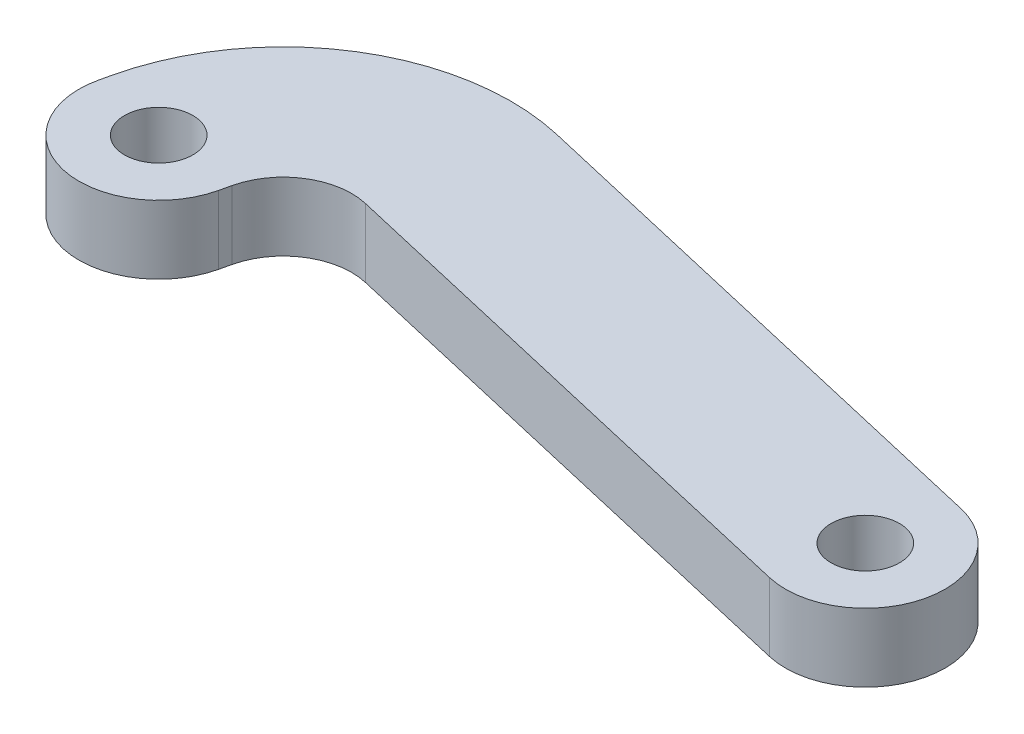
SolidWorks part; units mm, degrees
material "A-Glass Fiber"
ref_plane "Front Plane" through (0, 0, 0) normal (0, 0, 1) x (1, 0, 0)
ref_plane "Top Plane" through (0, 0, 0) normal (0, 1, 0) x (1, 0, 0)
ref_plane "Right Plane" through (0, 0, 0) normal (1, 0, 0) x (0, 0, -1)
sketch "Sketch1" plane through (0, 0, 0) normal (0, 1, 0) x (1, 0, 0)
  line L0 (3.4096, -0.7903) -> (3.5225, -0.3032)
  line L3 (7.1224, 1.9419) -> (30.2097, -3.4096)
  line L4 (-3.4096, 0.7903) -> (-3.2967, 1.2774)
  line L5 (8.7031, 8.7611) -> (31.7903, 3.4096)
  circle A2 centre (0, 0) radius 1.5
  circle A3 centre (31, 0) radius 1.5
  arc A4 (30.2097, -3.4096) -> (31.7903, 3.4096) centre (31, 0) ccw
  arc A5 (3.4096, -0.7903) -> (-3.4096, 0.7903) centre (0, 0) cw
  arc A6 (-3.2967, 1.2774) -> (8.7031, 8.7611) centre (6.445, -0.9807) cw
  arc A7 (3.5225, -0.3032) -> (7.1224, 1.9419) centre (6.445, -0.9807) cw
  dimension "D2" = 3
  dimension "D3" = 7
  dimension "D5" = 3
  dimension "D6" = 10
  dimension "D1" = 31
  dimension "D4" = 3.5
extrude "Boss-Extrude1" add sketch "Sketch1" along normal blind 3
